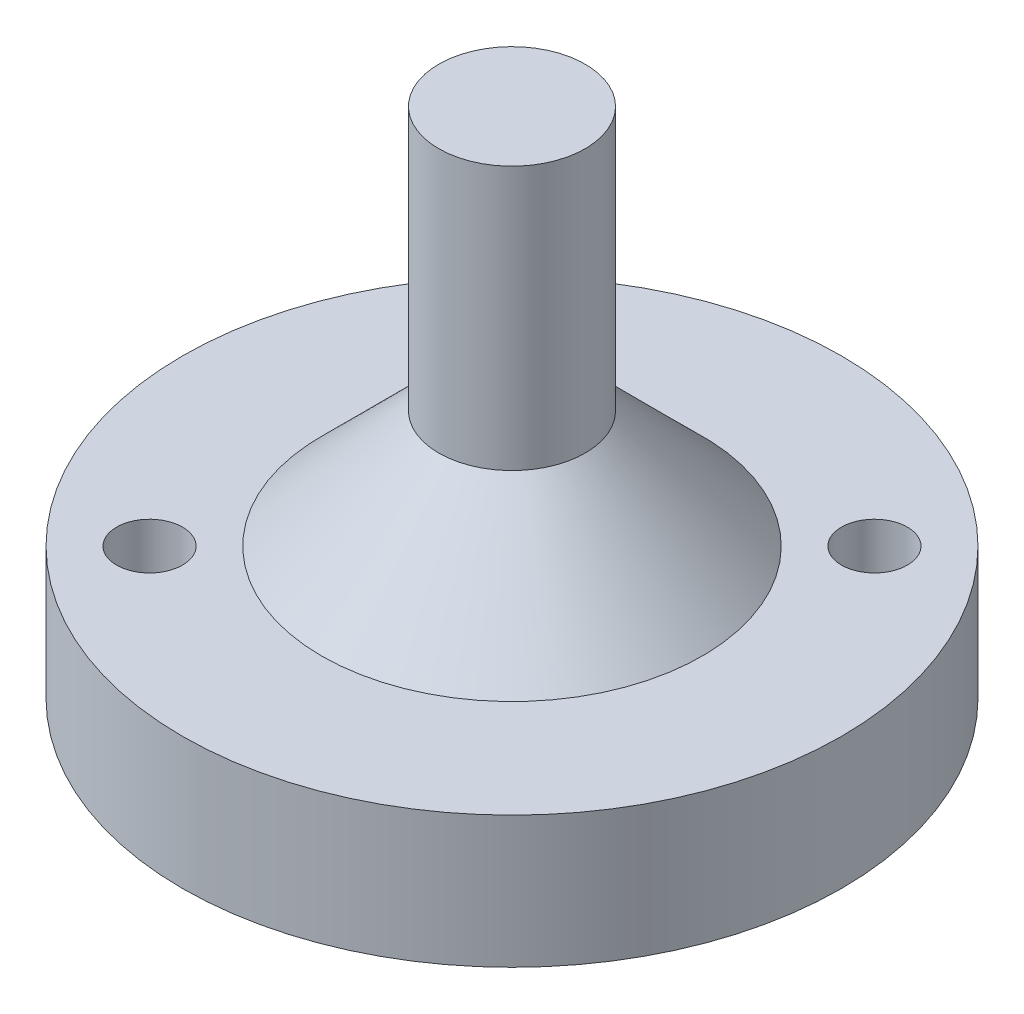
SolidWorks part; units mm, degrees
ref_plane "Front Plane" through (0, 0, 0) normal (0, 0, 1) x (1, 0, 0)
ref_plane "Top Plane" through (0, 0, 0) normal (0, 1, 0) x (1, 0, 0)
ref_plane "Right Plane" through (0, 0, 0) normal (1, 0, 0) x (0, 0, -1)
sketch "Sketch1" plane through (0, 0, 0) normal (0, 1, 0) x (1, 0, 0)
  circle A0 centre (0, 0) radius 22.5
  dimension "D1" = 45
extrude "Boss-Extrude1" add sketch "Sketch1" along normal blind 9
sketch "Sketch2" plane through (0, 9, 0) normal (0, 1, 0) x (1, 0, 0)
  line L0 (0, 0) -> (12.3744, 12.3744) construction
  circle A0 centre (0, 0) radius 17.5 construction
  circle A1 centre (12.3744, 12.3744) radius 2.25
  dimension "D1" = 35
  dimension "D2" = 4.5
extrude "Cut-Extrude1" cut sketch "Sketch2" against normal through all
pattern_circular "CirPattern1" count 2 over 360 about axis through (0, 0, 0) along (0, 1, 0) of "Cut-Extrude1"
sketch "Sketch3" plane through (0, 9, 0) normal (0, 1, 0) x (1, 0, 0)
  circle A0 centre (0, 0) radius 5
  dimension "D1" = 10
extrude "Boss-Extrude2" add sketch "Sketch3" along normal blind 26
chamfer "Chamfer1" distance 8 angle 45 1 edges at (0, 9, 5)
sketch "Sketch6" plane through (0, 0, 0) normal (0, -1, 0) x (1, 0, 0)
  circle A0 centre (0, 0) radius 9.25
  dimension "D1" = 18.5
extrude "Cut-Extrude4" cut sketch "Sketch6" against normal blind 7
